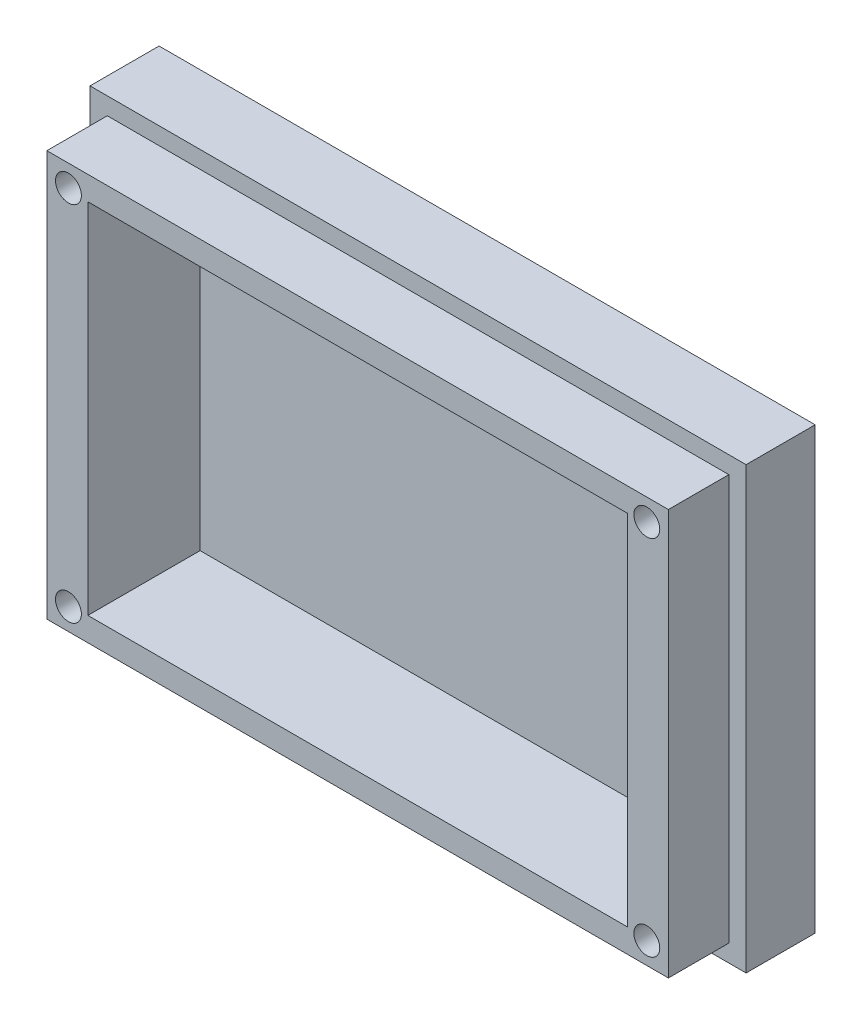
SolidWorks part; units mm, degrees
ref_plane "正面" through (0, 0, 0) normal (0, 0, 1) x (1, 0, 0)
ref_plane "平面" through (0, 0, 0) normal (0, 1, 0) x (1, 0, 0)
ref_plane "右側面" through (0, 0, 0) normal (1, 0, 0) x (0, 0, -1)
sketch "ｽｹｯﾁ1" plane through (0, 0, 0) normal (0, 0, 1) x (1, 0, 0)
  line L1 (-33.9727, 27.3979) -> (38.0273, 27.3979)
  line L2 (-33.9727, 27.3979) -> (-33.9727, -19.6021)
  line L3 (-33.9727, -19.6021) -> (38.0273, -19.6021)
  line L4 (38.0273, 27.3979) -> (38.0273, -19.6021)
  dimension "D1" = 72
  dimension "D2" = 47
extrude "ﾎﾞｽ - 押し出し1" add sketch "ｽｹｯﾁ1" along normal blind 15
sketch "ｽｹｯﾁ2" plane through (0, 0, 15) normal (0, 0, 1) x (1, 0, 0)
  line L0 (38.0273, 27.3979) -> (-33.9727, 27.3979) construction
  line L1 (-29.2227, 24.6479) -> (33.2773, 24.6479)
  line L2 (-29.2227, 24.6479) -> (-29.2227, -16.8521)
  line L3 (-29.2227, -16.8521) -> (33.2773, -16.8521)
  line L4 (33.2773, 24.6479) -> (33.2773, -16.8521)
  line L5 (-33.9727, 27.3979) -> (-33.9727, -19.6021) construction
  dimension "D1" = 62.5
  dimension "D2" = 41.5
  dimension "D3" = 2.75
  dimension "D4" = 4.75
extrude "ｶｯﾄ - 押し出し1" cut sketch "ｽｹｯﾁ2" against normal blind 13
sketch "ｽｹｯﾁ3" plane through (0, 0, 15) normal (0, 0, 1) x (1, 0, 0)
  line L0 (38.0273, 27.3979) -> (-33.9727, 27.3979) construction
  line L1 (-33.9727, 27.3979) -> (-33.9727, -19.6021) construction
  circle A0 centre (-31.4727, 24.8979) radius 1.5
  circle A1 centre (35.5273, 24.8979) radius 1.5
  circle A2 centre (-31.4727, -17.1021) radius 1.5
  circle A3 centre (35.5273, -17.1021) radius 1.5
  dimension "D1" = 3
  dimension "D2" = 2.5
  dimension "D3" = 2.5
  dimension "D4" = 2
  dimension "D5" = 2
extrude "ｶｯﾄ - 押し出し3" cut sketch "ｽｹｯﾁ3" against normal through all
sketch "ｽｹｯﾁ4" plane through (0, 0, 0) normal (0, 0, -1) x (-1, 0, 0)
  line L1 (-40.0273, 29.3979) -> (35.9727, 29.3979)
  line L2 (-40.0273, 29.3979) -> (-40.0273, -21.6021)
  line L3 (-40.0273, -21.6021) -> (35.9727, -21.6021)
  line L4 (35.9727, 29.3979) -> (35.9727, -21.6021)
  line L5 (-38.0273, 27.3979) -> (33.9727, 27.3979)
  line L6 (-38.0273, 27.3979) -> (-38.0273, -19.6021)
  line L7 (-38.0273, -19.6021) -> (33.9727, -19.6021)
  line L8 (33.9727, 27.3979) -> (33.9727, -19.6021)
  dimension "D1" = 2
  dimension "D2" = 2
  dimension "D3" = 2
  dimension "D4" = 2
extrude "ﾎﾞｽ - 押し出し2" add sketch "ｽｹｯﾁ4" against normal blind 8
